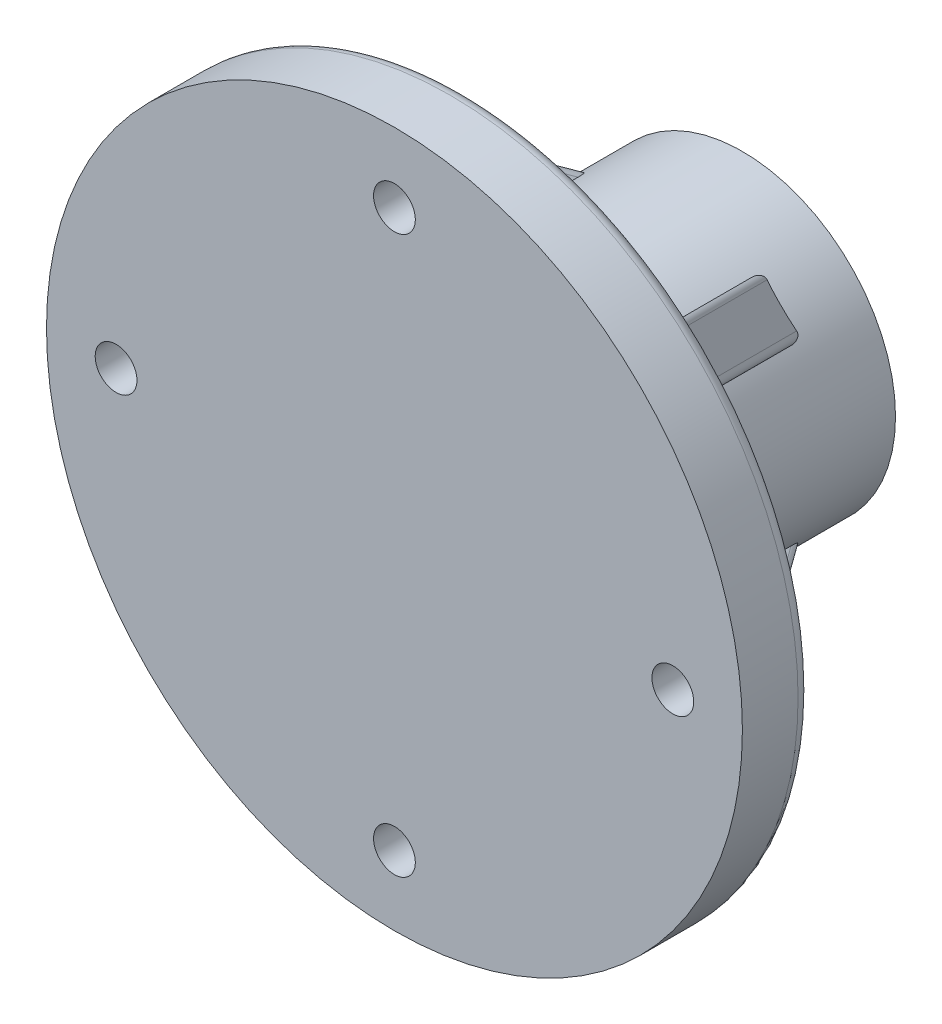
SolidWorks part; units mm, degrees
ref_plane "Спереди" through (0, 0, 0) normal (0, 0, 1) x (1, 0, 0)
ref_plane "Сверху" through (0, 0, 0) normal (0, 1, 0) x (1, 0, 0)
ref_plane "Справа" through (0, 0, 0) normal (1, 0, 0) x (0, 0, -1)
other "Configuration Table"
sketch "Sketch1" plane through (0, 0, 0) normal (0, 0, 1) x (1, 0, 0)
  circle A0 centre (0, 0) radius 11
  dimension "D1" = 22
extrude "Boss-Extrude1" add sketch "Sketch1" along normal blind 20 contours A0
sketch "Sketch5" plane through (0, 0, 20) normal (0, 0, 1) x (1, 0, 0)
  circle A0 centre (0, 0) radius 25
  dimension "D1" = 50
extrude "Boss-Extrude2" add sketch "Sketch5" along normal blind 5
sketch "Sketch6" plane through (0, 0, 20) normal (0, 0, -1) x (-1, 0, 0)
  line L0 (-25, 0) -> (25, 0) construction
  line L1 (0, 25) -> (0, -25) construction
  line L2 (-17.6777, -17.6777) -> (17.6777, 17.6777) construction
  line L3 (17.6777, -17.6777) -> (-17.6777, 17.6777) construction
  circle A0 centre (0, 0) radius 25 construction
  circle A1 centre (0, 20) radius 1.5
  circle A2 centre (0, -20) radius 1.5
  circle A3 centre (-20, 0) radius 1.5
  circle A4 centre (20, 0) radius 1.5
  dimension "D3" = 3
  dimension "D1" = 45
  dimension "D2" = 45
  dimension "D4" = 40
  dimension "D5" = 40
extrude "Cut-Extrude2" cut sketch "Sketch6" against normal up to next
fillet "Fillet2" radius 5 1 edges at (11, 0, 20)
ref_plane "Plane1" through (0, 0, 0) normal (-0.7071, 0.7071, 0) x (0.7071, 0.7071, 0)
sketch "Sketch12" plane through (0, 0, 0) normal (-0.7071, 0.7071, 0) x (0.7071, 0.7071, 0)
  line L0 (11, -5) -> (23, -20)
  line L1 (11, -15) -> (11, 0) construction
  line L2 (25, -20) -> (-25, -20) construction
  dimension "D1" = 15
  dimension "D2" = 12
rib "Rib10" sketch "Sketch12" sketch "Sketch12" thickness 4 extrusion direction parallel to sketch draft on no parameters "D1"=4
pattern_circular "CirPattern1" count 4 over 360 about axis through (0, 0, 0) along (0, 0, 1) of "Rib10"
fillet "Fillet3" radius 1 1 edges at (25, 0, 20)
fillet "Fillet4" radius 0.5 8 edges at (10.5418, -13.3702, 12.3854) (13.3702, -10.5418, 12.3854) (-10.5418, -13.3702, 12.3854) (-13.3702, -10.5418, 12.3854) (13.3702, 10.5418, 12.3854) (10.5418, 13.3702, 12.3854) (-13.3702, 10.5418, 12.3854) (-10.5418, 13.3702, 12.3854)
sketch "Sketch13" plane through (0, 0, 20) normal (0, 0, -1) x (-1, 0, 0)
  circle A0 centre (-20, 0) radius 3
  circle A1 centre (0, 20) radius 3
  circle A2 centre (20, 0) radius 3
  circle A3 centre (0, -20) radius 3
  dimension "D1" = 6
extrude "Cut-Extrude3" cut sketch "Sketch13" against normal blind 1
sketch "Sketch14" plane through (0, 0, 0) normal (0, 0, -1) x (-1, 0, 0)
  line L0 (0, 0) -> (27.9499, 0) construction
  line L1 (0, 0) -> (0, 26.4718) construction
  line L2 (0, 0) -> (19.8539, 19.8539) construction
  line L3 (-7.2562, 7.2562) -> (6.6515, -6.6515) construction
  circle A0 centre (-5.6569, 5.6569) radius 1.5
  circle A1 centre (5.6569, -5.6569) radius 1.5
  circle A2 centre (5.6569, 5.6569) radius 1.5
  circle A3 centre (-5.6569, -5.6569) radius 1.5
  dimension "D2" = 3
  dimension "D3" = 16
  dimension "D4" = 16
  dimension "D1" = 45
extrude "Cut-Extrude4" cut sketch "Sketch14" against normal blind 12
